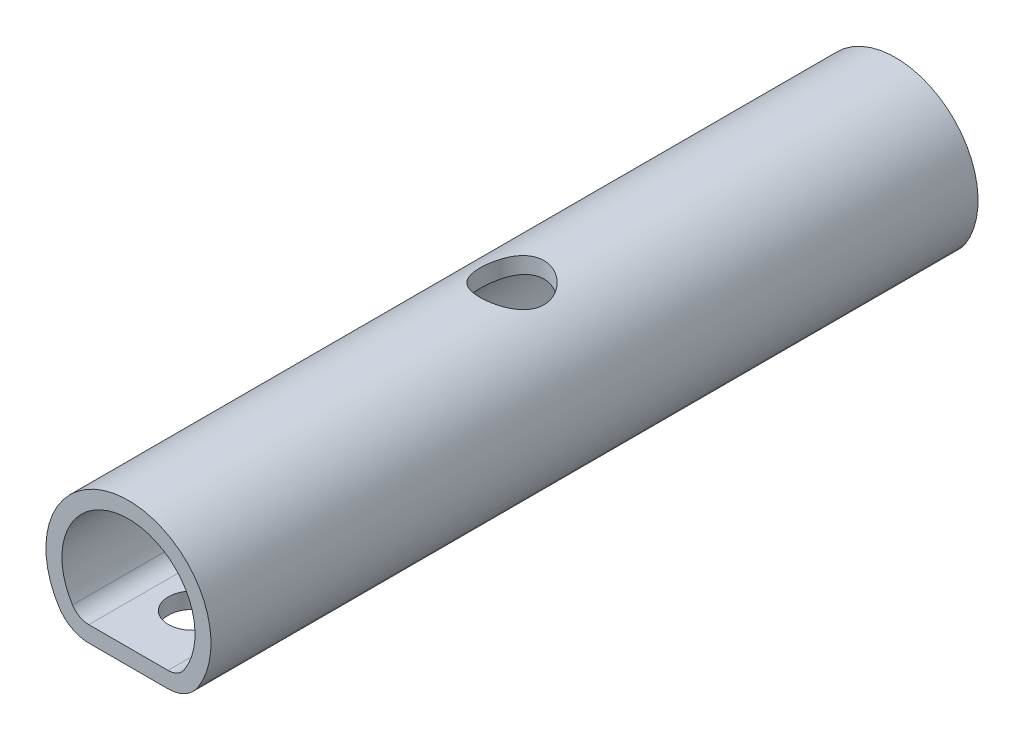
SolidWorks part; units mm, degrees
ref_plane "Front Plane" through (0, 0, 0) normal (0, 0, 1) x (1, 0, 0)
ref_plane "Top Plane" through (0, 0, 0) normal (0, 1, 0) x (1, 0, 0)
ref_plane "Right Plane" through (0, 0, 0) normal (1, 0, 0) x (0, 0, -1)
ref_plane "Plane4" through (0, 0, -38.1) normal (0, 0, -1) x (-1, 0, 0)
sketch "Sketch1" plane through (0, 0, -38.1) normal (0, 0, -1) x (-1, 0, 0)
  line L0 (-5.5333, 4.9784) -> (5.5333, 4.9784)
  arc A0 (5.5333, 4.9784) -> (-5.5333, 4.9784) centre (0, 11.0287) ccw
extrude "Boss-Extrude1" add sketch "Sketch1" against normal blind 76.2
sketch "Sketch2" plane through (0, 0, 38.1) normal (0, 0, 1) x (1, 0, 0)
  line L0 (-4.8781, 6.5659) -> (4.8781, 6.5659)
  arc A0 (4.8781, 6.5659) -> (-4.8781, 6.5659) centre (0, 11.0287) ccw
extrude "Cut-Extrude1" cut sketch "Sketch2" against normal through all
hole_wizard "M4 Clearance Hole1" positions "Sketch4" profile "Sketch3" hole size "M4" standard "ANSI Metric"
sketch "Sketch4" plane through (0, 4.9784, 0) normal (0, -1, 0) x (-1, 0, 0)
  point P0 (0, 0)
  point P1 (0, 31.75)
  point P2 (0, -31.75)
sketch "Sketch3" plane through (0, 4.9784, 0) normal (1, 0, 0) x (0, 0, -1)
  line L0 (0, 0) -> (0, 1.5875)
  line L1 (0, 1.5875) -> (2.3876, 1.5875)
  line L2 (2.3876, 1.5875) -> (2.3876, 0)
  line L5 (2.3876, 0) -> (0, 0)
  line L11 (0, -6.35) -> (0, 107.95) construction
  dimension "Thru Hole Dia." = 4.7752
  dimension "Thru Hole Depth" = 1.5875
hole_wizard "Hole1" positions "3DSketch1" profile "Sketch5" legacy
sketch3d "3DSketch1"
  point P0 (0, 19.2278, 0)
  point P1 (0, 19.2278, -31.75)
  point P2 (0, 19.2278, 31.75)
sketch "Sketch5" plane through (0, 19.2278, 0) normal (1, 0, 0) x (0, 0, 1)
  line L0 (0, 0) -> (0, 14.2494)
  line L1 (0, 14.2494) -> (3.175, 14.2494)
  line L2 (3.175, 14.2494) -> (3.175, 0)
  line L3 (3.175, 0) -> (0, 0)
  line L4 (0, 110) -> (0, -10) construction
  dimension "Diameter" = 6.35
  dimension "Depth" = 14.2494
fillet "Fillet1" radius 1.9304 2 edges at (4.8781, 6.5659, 0) (-4.8781, 6.5659, 0)
fillet "Fillet2" radius 3.5179 2 edges at (5.5333, 4.9784, 0) (-5.5333, 4.9784, 0)
